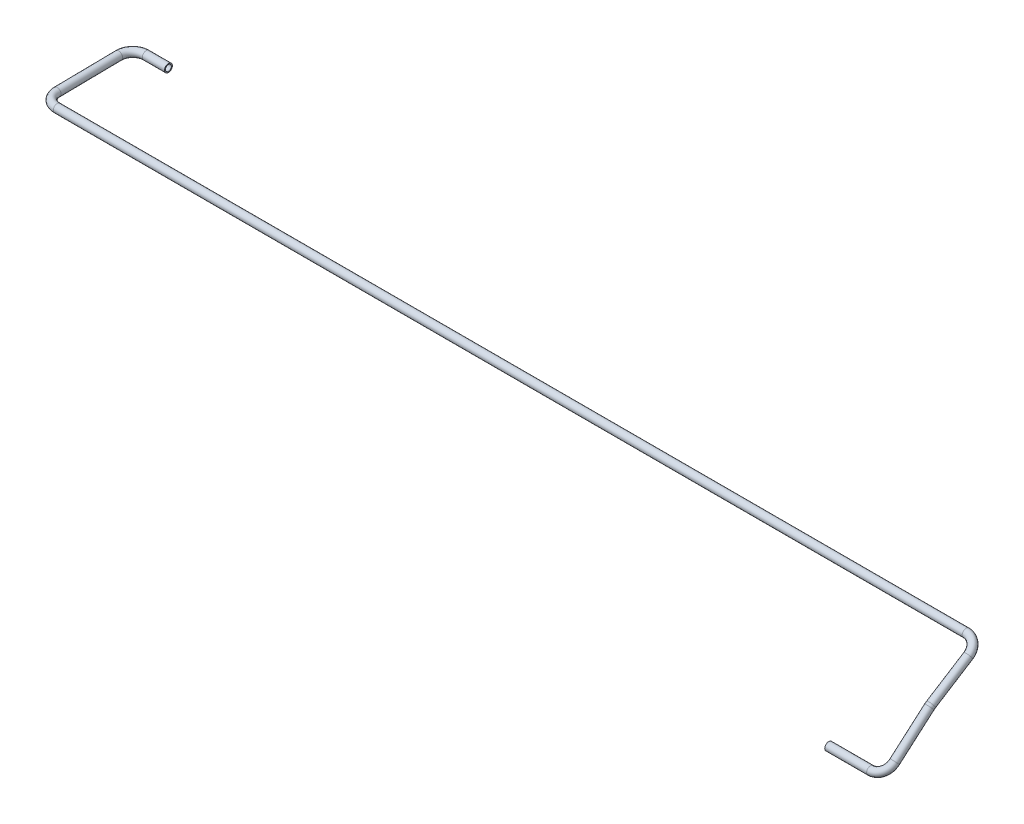
SolidWorks part; units mm, degrees
ref_plane "Plane1" through (0, 0, 0) normal (0, 0, 1) x (1, 0, 0)
ref_plane "Plane2" through (0, 0, 0) normal (0, 1, 0) x (1, 0, 0)
ref_plane "Plane3" through (0, 0, 0) normal (1, 0, 0) x (0, 0, -1)
sketch3d "3DSketch1"
  line L0 (0, 0, 0) -> (64, 0, 0)
  line L1 (85, 0, 0) -> (85, 61, 0) construction
  line L2 (85, 61, 0) -> (85, 61, -70) construction
  line L3 (85, 13.7965, -15.8321) -> (85, 59.9391, -68.7826)
  line L4 (85, 61, -70) -> (85, 109, -70) construction
  line L5 (85, 109, -70) -> (85, 109, -146) construction
  line L6 (85, 61.8623, -71.3653) -> (85, 97.7861, -128.2447)
  line L7 (64, 109, -146) -> (-1325, 109, -146)
  line L8 (-1346, 109, -146) -> (-1346, 111, -146) construction
  line L9 (-1346, 111, -146) -> (-1346, 111, -282) construction
  line L10 (-1346, 109.3088, -166.9977) -> (-1346, 110.6912, -261.0023)
  line L11 (-1325, 111, -282) -> (-1291, 111, -282)
  arc A0 (64, 0, 0) -> (85, 13.7965, -15.8321) centre (64, 13.7965, -15.8321) ccw
  arc A1 (85, 61.8623, -71.3653) -> (85, 59.9391, -68.7826) centre (85, 44.107, -82.5791) ccw
  arc A2 (64, 109, -146) -> (85, 97.7861, -128.2447) centre (64, 97.7861, -128.2447) ccw
  arc A3 (-1325, 111, -282) -> (-1346, 110.6912, -261.0023) centre (-1325, 110.6912, -261.0023) ccw
  arc A4 (-1325, 109, -146) -> (-1346, 109.3088, -166.9977) centre (-1325, 109.3088, -166.9977) ccw
  point P10 (85, 0, 0)
  point P12 (64, 29.6286, -2.0356)
  point P15 (85, 61, -70)
  point P17 (106, 44.107, -82.5791)
  point P20 (85, 109, -146)
  point P22 (64, 80.0309, -139.4586)
  point P27 (-1346, 111, -282)
  point P30 (-1325, 131.6889, -260.6935)
  point P33 (-1346, 109, -146)
  point P35 (-1325, 88.3111, -167.3065)
  dimension "D6" = 21
  dimension "D7" = 21
  dimension "D8" = 21
  dimension "D13" = 21
  dimension "D1" = 85
  dimension "D2" = 61
  dimension "D3" = 70
  dimension "D4" = 1431
  dimension "D10" = 55
  dimension "D5" = 76
  dimension "D9" = 48
  dimension "D11" = 136
  dimension "D12" = 2
ref_plane "Plane4" through (0, 0, 0) normal (1, 0, 0) x (0, 0, -1)
sketch "Sketch1" plane through (0, 0, 0) normal (1, 0, 0) x (0, 0, -1)
  circle A0 centre (0, 0) radius 6
  circle A1 centre (0, 0) radius 4.5
  dimension "D1" = 9
  dimension "D2" = 12
sweep "Sweep1" add profiles "Sketch1" path "3DSketch1"
